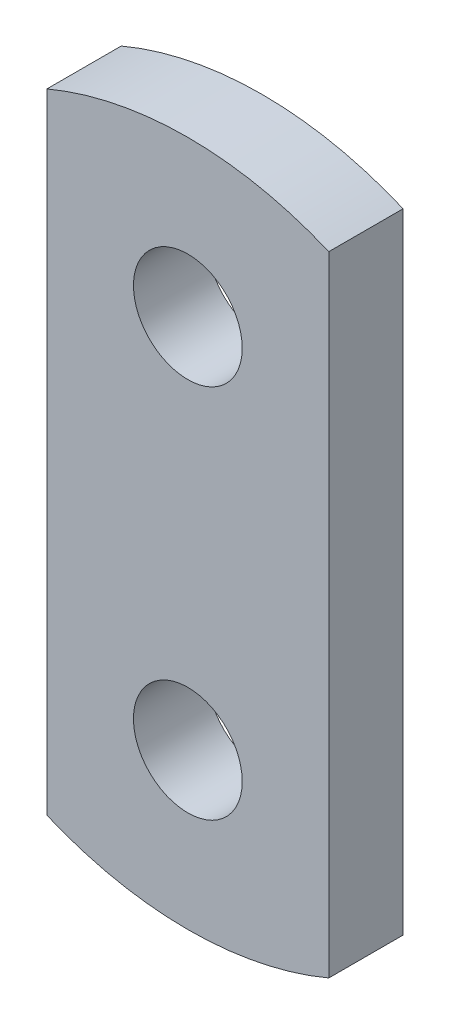
SolidWorks part; units mm, degrees
material "AISI 1045 Acero estirado en frío"
ref_plane "Alzado" through (0, 0, 0) normal (0, 0, 1) x (1, 0, 0)
ref_plane "Planta" through (0, 0, 0) normal (0, 1, 0) x (1, 0, 0)
ref_plane "Vista lateral" through (0, 0, 0) normal (1, 0, 0) x (0, 0, -1)
sketch "Croquis1" plane through (0, 0, 0) normal (0, 0, 1) x (1, 0, 0)
  line L0 (0, 0) -> (0, 69.4)
  line L2 (31.1, 69.4) -> (31.1, 0)
  line L4 (0, 34.7) -> (31.1, 34.7)
  line L5 (31.1, 34.7) -> (15.55, 34.7)
  line L6 (15.55, 34.7) -> (15.55, 72.55)
  line L7 (15.55, 34.7) -> (15.55, -3.15)
  arc A0 (0, 69.4) -> (31.1, 69.4) centre (15.55, 32.5937) cw
  arc A1 (0, 0) -> (31.1, 0) centre (15.55, 36.8063) ccw
  circle A2 centre (15.55, 55.4) radius 6
  circle A3 centre (15.55, 14) radius 6
  point P13 (15.55, -3.15)
  dimension "D5" = 12
  dimension "D6" = 12
  dimension "D7" = 20.7
  dimension "D8" = 20.7
  dimension "D1" = 69.4
  dimension "D2" = 31.1
  dimension "D3" = 37.85
  dimension "D4" = 37.85
extrude "Saliente-Extruir2" add sketch "Croquis1" along normal blind 8.2 contours A2 L6 A0 L0 L4 | A2 L6 L4 L2 A0 | A3 L7 L4 L0 A1 | A3 L7 A1 L2 L4
